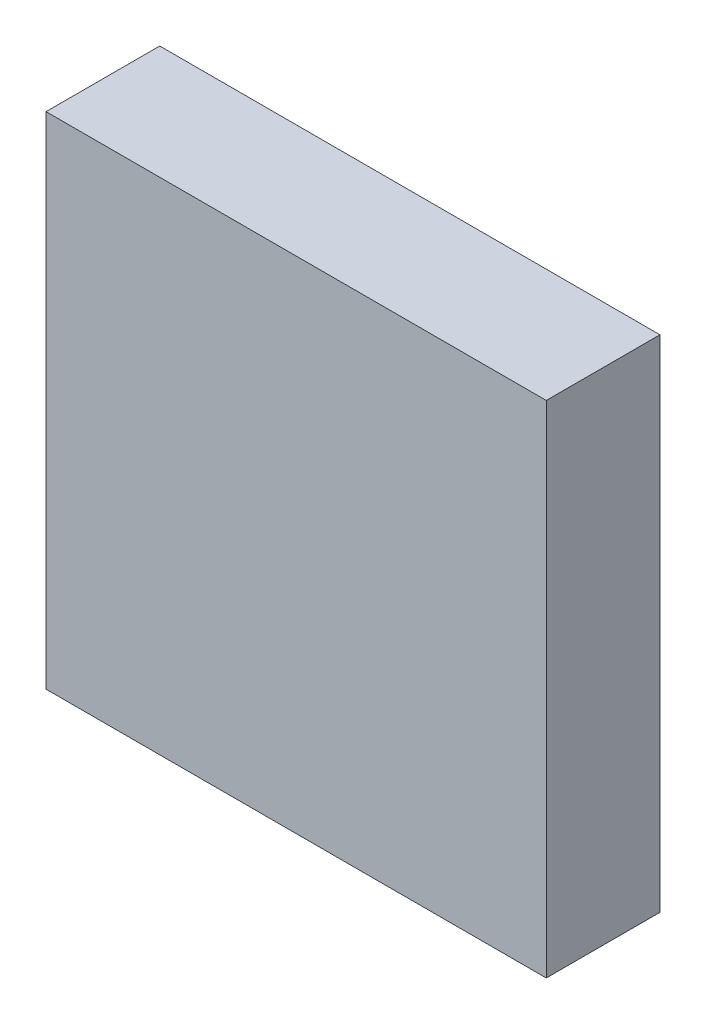
SolidWorks part; units mm, degrees
ref_plane "Front Plane" through (0, 0, 0) normal (0, 0, 1) x (1, 0, 0)
ref_plane "Top Plane" through (0, 0, 0) normal (0, 1, 0) x (1, 0, 0)
ref_plane "Right Plane" through (0, 0, 0) normal (1, 0, 0) x (0, 0, -1)
sketch "Sketch1" plane through (0, 0, 0) normal (0, 0, 1) x (1, 0, 0)
  line L1 (-5.5, -5.5) -> (5.5, -5.5)
  line L2 (-5.5, -5.5) -> (-5.5, 5.5)
  line L3 (-5.5, 5.5) -> (5.5, 5.5)
  line L4 (5.5, -5.5) -> (5.5, 5.5)
  line L5 (-5.5, -5.5) -> (5.5, 5.5) construction
  line L6 (-5.5, 5.5) -> (5.5, -5.5) construction
  point P0 (0, 0)
  dimension "D1" = 11
extrude "Boss-Extrude1" add sketch "Sketch1" along normal mid plane 2.5
